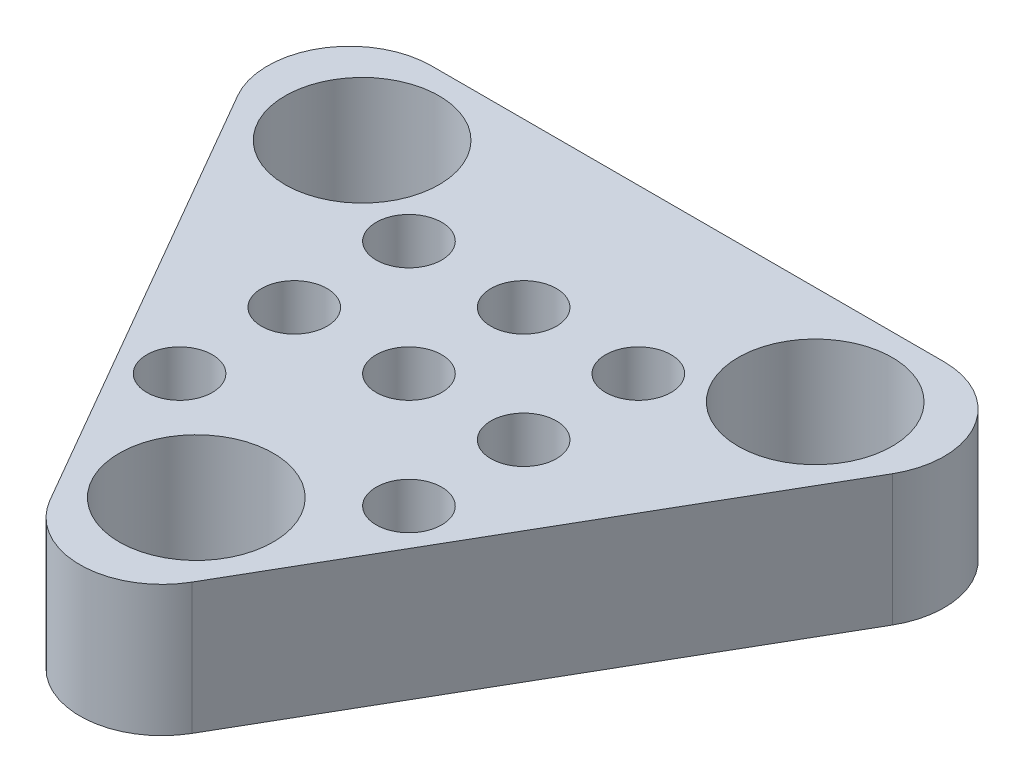
SolidWorks part; units mm, degrees
material "Chrome Stainless Steel"
ref_plane "Front Plane" through (0, 0, 0) normal (0, 0, 1) x (1, 0, 0)
ref_plane "Top Plane" through (0, 0, 0) normal (0, 1, 0) x (1, 0, 0)
ref_plane "Right Plane" through (0, 0, 0) normal (1, 0, 0) x (0, 0, -1)
sketch "Sketch1" plane through (0, 0, 0) normal (0, 1, 0) x (1, 0, 0)
  line L0 (-5.186, 3.3162) -> (2.6377, -10.235)
  line L1 (6.9679, -10.235) -> (14.7916, 3.3162)
  line L2 (12.6266, 7.0662) -> (-3.021, 7.0662)
  line L3 (-1.2742, -3.4594) -> (15.2246, 6.0662) construction
  line L4 (4.8028, 7.0662) -> (4.8028, -11.985) construction
  line L5 (10.8797, -3.4594) -> (-5.6191, 6.0662) construction
  circle A0 centre (-2.1106, 4.0406) radius 2.35
  circle A4 centre (4.8028, -7.9338) radius 2.35
  circle A5 centre (11.7162, 4.0406) radius 2.35
  circle A6 centre (1.2703, 2.0886) radius 1
  circle A7 centre (4.7703, 2.0886) radius 1
  circle A8 centre (8.2703, 2.0886) radius 1
  circle A9 centre (1.2703, -1.4114) radius 1
  circle A10 centre (4.7703, -1.4114) radius 1
  circle A11 centre (8.2703, -1.4114) radius 1
  circle A12 centre (1.2703, -4.9114) radius 1
  circle A13 centre (4.7703, -4.9114) radius 1 [skipped]
  circle A14 centre (8.2703, -4.9114) radius 1
  arc A15 (-5.186, 3.3162) -> (-3.021, 7.0662) centre (-3.021, 4.5662) cw
  arc A16 (14.7916, 3.3162) -> (12.6266, 7.0662) centre (12.6266, 4.5662) ccw
  arc A17 (6.9679, -10.235) -> (2.6377, -10.235) centre (4.8028, -8.985) cw
  point P9 (-7.3511, 7.0662)
  point P12 (4.8028, -13.985)
  point P22 (4.8028, 0.0491)
  dimension "D1" = 4.7
  dimension "D9" = 4.7
  dimension "D10" = 4.7
  dimension "D11" = 2
  dimension "D12" = 2.5
  dimension "D2" = 300
  dimension "D3" = 60
  dimension "D4" = 24.3078
  dimension "D6" = 15
  dimension "D7" = 15
  dimension "D8" = 15
extrude "Extrude1" add sketch "Sketch1" along normal blind 4
